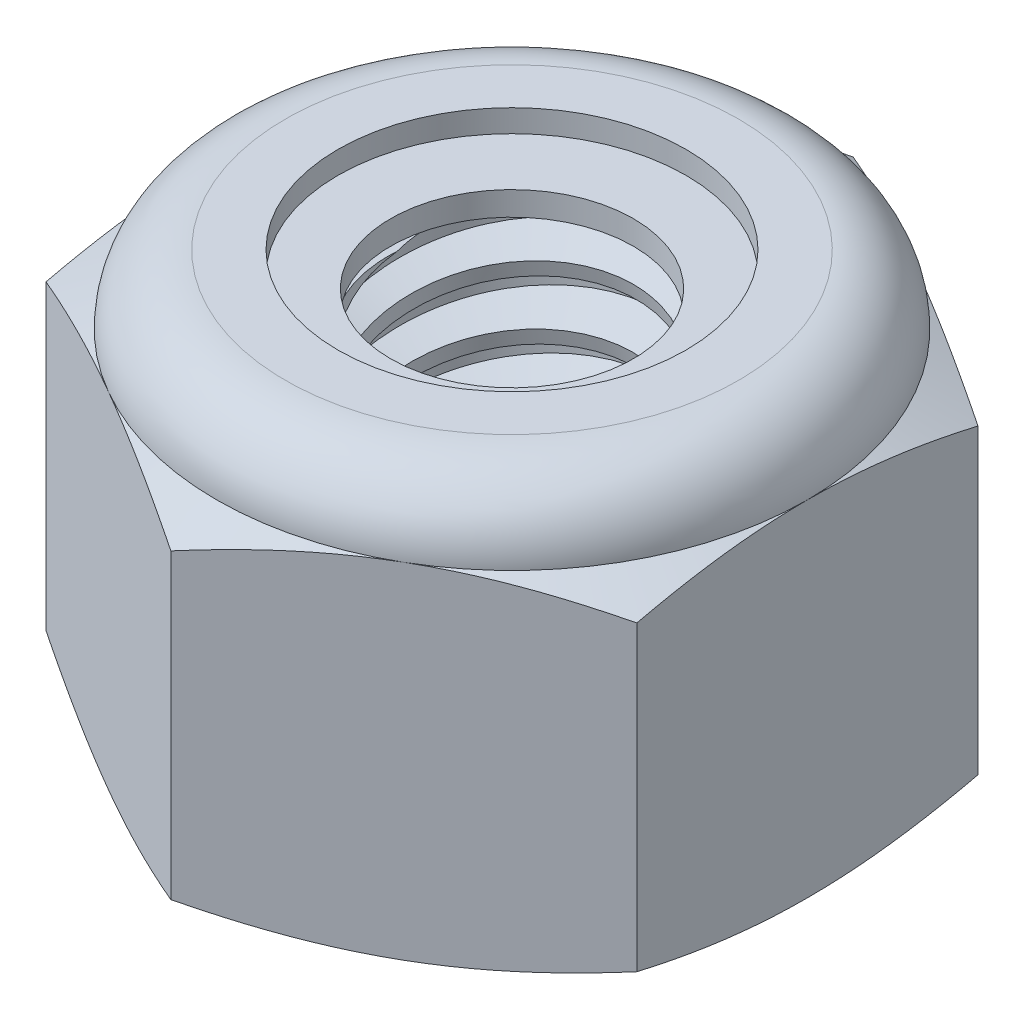
SolidWorks part; units mm, degrees
material "18-8 Stainless Steel"
ref_plane "Front" through (0, 0, 0) normal (0, 0, 1) x (1, 0, 0)
ref_plane "Top" through (0, 0, 0) normal (0, 1, 0) x (1, 0, 0)
ref_plane "Right" through (0, 0, 0) normal (1, 0, 0) x (0, 0, -1)
sketch "Sketch1" plane through (0, 0, 0) normal (0, 1, 0) x (1, 0, 0)
  line L1 (0, 2.3094) -> (-2, 1.1547)
  line L2 (-2, 1.1547) -> (-2, -1.1547)
  line L3 (-2, -1.1547) -> (0, -2.3094)
  line L4 (0, -2.3094) -> (2, -1.1547)
  line L5 (2, -1.1547) -> (2, 1.1547)
  line L6 (2, 1.1547) -> (0, 2.3094)
  circle A0 centre (0, 0) radius 2 construction
  dimension "Hex Flats" = 4
extrude "Extrude1" add sketch "Sketch1" along normal blind 2.8
sketch "Sketch2" plane through (0, 0, 0) normal (1, 0, 0) x (0, 0, -1)
  line L0 (-1, 0) -> (-1, 2.8) construction
  line L1 (0, 0) -> (1, 0)
  line L2 (0, 0) -> (0, 2.8)
  line L3 (0, 2.8) -> (1, 2.8)
  line L4 (1, 0) -> (1, 2.8)
  line L5 (-1.1547, 2.8) -> (1.1547, 2.8) construction
  line L7 (0, -1) -> (0, 0) construction
  dimension "Thread Dia" = 2
revolve "Revolve1" add sketch "Sketch2" angle 360 about L7
sketch "Sketch3" plane through (0, 0, 0) normal (1, 0, 0) x (0, 0, -1)
  line L0 (1, 2.8) -> (-1, 2.8) construction
  line L1 (-1, 2.8) -> (-1, 2.4) construction
  line L2 (-1, 2.4) -> (1, 2.8) construction
  line L3 (1, 2.8) -> (1.0098, 2.751) construction
  line L4 (1.0098, 2.751) -> (1.0784, 2.4078)
  line L5 (1.0784, 2.4078) -> (0.8416, 2.4879)
  line L6 (0.8416, 2.4879) -> (0.822, 2.5859)
  line L7 (0.822, 2.5859) -> (1.0098, 2.751)
  line L8 (0.8318, 2.5369) -> (1.0441, 2.5794) construction
  line L9 (1, 2.8) -> (1, 2.5705) construction
  line L10 (1, 2.5705) -> (-1, 2.1705) construction
  line L11 (-1, 2.1705) -> (-1, 2.4) construction
  line L12 (-0.0859, 2.8) -> (0.0859, 1.9411) construction
  line L13 (-1, 0) -> (-1, 2.8) construction
  line L14 (0, 2.8) -> (1, 2.8) construction
  line L15 (1, 0) -> (1, 2.8) construction
  point P13 (0, 2.3705)
  dimension "D1" = 0.05
  dimension "D2" = 0.1
  dimension "Thread Pitch" = 0.4
  dimension "D4" = 60
  dimension "D5" = 0.4
revolve "Cut-Revolve1" cut sketch "Sketch3" angle 360 about L12
pattern_linear "LPattern1" count 7 spacing 0.4 along (0, -1, 0) count 2 spacing 0.4 along (0, 1, 0) of "Cut-Revolve1"
sketch "Sketch4" plane through (0, 0, 0) normal (1, 0, 0) x (0, 0, -1)
  line L0 (0, 2.8) -> (1, 2.8)
  line L1 (1, 2.8) -> (0.822, 2.717)
  line L2 (0.822, 2.717) -> (0.822, 0.083)
  line L3 (0.822, 0.083) -> (1, 0)
  line L4 (1, 0) -> (0, 0)
  line L5 (0, 0) -> (0, 2.8)
  line L6 (1, 0) -> (1, 2.8) construction
  line L7 (0, 2.8) -> (1, 2.8) construction
  line L8 (0, 0) -> (1, 0) construction
  line L9 (0, 0) -> (0, 2.8) construction
  line L10 (0, 2.8) -> (0, 2.9964) construction
  dimension "D1" = 25
revolve "Cut-Revolve2" cut sketch "Sketch4" angle 360 about L10
combine bodies "Combine1" operation type subtract main body 112 bodies to subtract 111
sketch "Sketch5" plane through (0, 0, 0) normal (1, 0, 0) x (0, 0, -1)
  line L0 (0, 0) -> (2, 0)
  line L1 (2, 0) -> (2.3094, 0.1443)
  line L2 (2.3094, 0.1443) -> (2.3094, 2.1891)
  line L3 (2.3094, 2.1891) -> (2, 2.3333)
  line L4 (1.5333, 2.8) -> (1.5333, 4.07)
  line L5 (1.5333, 4.07) -> (3.5794, 4.07)
  line L6 (3.5794, 4.07) -> (3.5794, -1.27)
  line L7 (3.5794, -1.27) -> (0, -1.27)
  line L8 (0, -1.27) -> (0, 0)
  line L9 (2, 2.3333) -> (2, 0) construction
  line L10 (0, 0) -> (1, 0) construction
  line L13 (2.3094, 1.1667) -> (3.5794, 1.1667) construction
  line L14 (2.3094, 2.8) -> (2.3094, 0) construction
  line L15 (0, 0) -> (0, 4.07) construction
  line L20 (0, 4.07) -> (1.5333, 4.07) construction
  line L22 (0, 2.8) -> (1, 2.8) construction
  arc A0 (2, 2.3333) -> (1.5333, 2.8) centre (1.5333, 2.3333) ccw
  dimension "D1" = 25
  dimension "D2" = 1.27
  dimension "D3" = 2.8
  dimension "D4" = 0.4667
revolve "Cut-Revolve3" cut sketch "Sketch5" angle 360 about L15
sketch "Sketch6" plane through (0, 0, 0) normal (1, 0, 0) x (0, 0, -1)
  line L0 (0, 2.3333) -> (1.8476, 2.3333)
  line L1 (1.5333, 2.6476) -> (1.1777, 2.6476)
  line L2 (0, 4.07) -> (0, 2.3333)
  line L3 (1.1777, 4.07) -> (0, 4.07)
  line L4 (0, 4.07) -> (1.5333, 4.07) construction
  line L5 (0, 0) -> (0, 4.07) construction
  line L6 (0, 4.07) -> (0, 44.323) construction
  line L7 (1.1777, 2.6476) -> (1.1777, 4.07)
  line L8 (1.5333, 2.8) -> (1.5333, 2.6476) construction
  line L9 (1.1777, 2.6476) -> (0.822, 2.6476) construction
  line L10 (0.822, 2.6476) -> (0.822, 2.717) construction
  arc A0 (1.8476, 2.3333) -> (1.5333, 2.6476) centre (1.5333, 2.3333) ccw
  arc A1 (2, 2.3333) -> (1.5333, 2.8) centre (1.5333, 2.3333) ccw construction
  dimension "D1" = 0.1524
revolve "Cut-Revolve4" cut sketch "Sketch6" angle 360 about L6
sketch "Sketch7" plane through (0, 0, 0) normal (1, 0, 0) x (0, 0, -1)
  line L0 (0.822, 2.4095) -> (1.7589, 2.4095)
  line L1 (1.5333, 2.5714) -> (0.822, 2.5714)
  line L2 (0.822, 2.5714) -> (0.822, 2.4095)
  line L3 (0.822, 2.4095) -> (0, 2.4095) construction
  line L4 (0, 2.4095) -> (0, 2.5714) construction
  line L5 (0, 2.5714) -> (0.822, 2.5714) construction
  line L6 (0.822, 2.4095) -> (0.822, 2.3333) construction
  line L7 (0, 2.3333) -> (1.8476, 2.3333) construction
  line L8 (1.5333, 2.5714) -> (1.5333, 2.6476) construction
  arc A0 (1.7589, 2.4095) -> (1.5333, 2.5714) centre (1.5333, 2.3333) ccw
  arc A2 (1.8476, 2.3333) -> (1.5333, 2.6476) centre (1.5333, 2.3333) ccw construction
  dimension "D1" = 0.0762
revolve "Revolve2" add sketch "Sketch7" angle 360 about L4
equation "\"D1@Sketch3\"=\"Thread Pitch@Sketch3\"/8"
equation "\"D2@Sketch3\"=\"Thread Pitch@Sketch3\"/4"
equation "\"D5@Sketch3\"=\"Thread Pitch@Sketch3\""
equation "\"D4@LPattern1\"=\"Thread Pitch@Sketch3\""
equation "\"D3@LPattern1\"=\"Thread Pitch@Sketch3\""
equation "\"D1@LPattern1\"=\"Height@Extrude1\"/\"Thread Pitch@Sketch3\""
equation "\"D4@Sketch5\"=\"Height@Extrude1\"/6"
